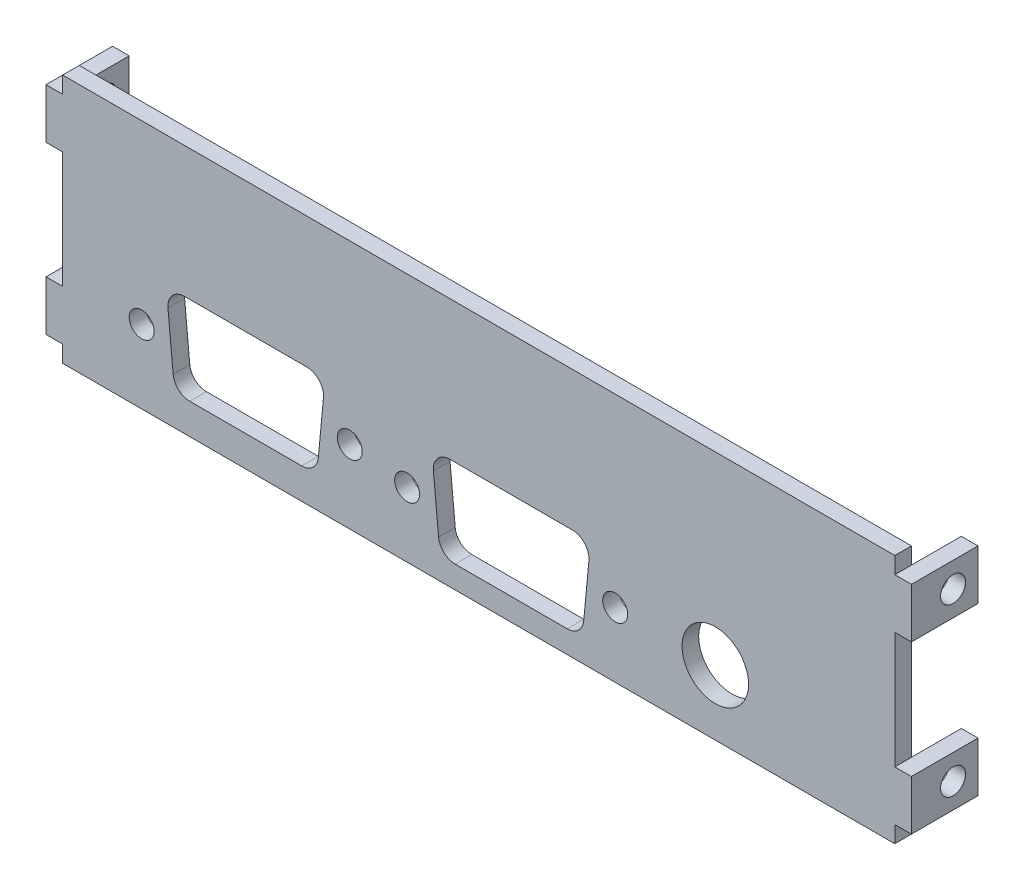
SolidWorks part; units mm, degrees
ref_plane "Front Plane" through (0, 0, 0) normal (0, 0, 1) x (1, 0, 0)
ref_plane "Top Plane" through (0, 0, 0) normal (0, 1, 0) x (1, 0, 0)
ref_plane "Right Plane" through (0, 0, 0) normal (1, 0, 0) x (0, 0, -1)
sketch "Sketch1" plane through (0, 0, 0) normal (0, 0, 1) x (1, 0, 0)
  line L1 (-50, -15) -> (50, -15)
  line L2 (-50, -15) -> (-50, 15)
  line L3 (-50, 15) -> (50, 15)
  line L4 (50, -15) -> (50, 15)
  line L5 (-50, -15) -> (50, 15) construction
  line L6 (-50, 15) -> (50, -15) construction
  point P0 (0, 0)
  dimension "D1" = 30
  dimension "D2" = 100
extrude "Boss-Extrude1" add sketch "Sketch1" along normal blind 2
sketch "Sketch2" plane through (0, 0, 2) normal (0, 0, 1) x (1, 0, 0)
  line L0 (-50, 15) -> (-50, -15) construction
  line L1 (-50, 13) -> (-52, 13)
  line L2 (-50, 13) -> (-50, 7)
  line L3 (-50, 7) -> (-52, 7)
  line L4 (-52, 13) -> (-52, 7)
  line L5 (-51, 7) -> (-51, 13) construction
  line L6 (-50, 10) -> (-52, 10) construction
  line L7 (50, -15) -> (50, 15) construction
  line L8 (-50, -7) -> (-52, -7)
  line L9 (-50, -7) -> (-50, -13)
  line L10 (-50, -13) -> (-52, -13)
  line L11 (-52, -7) -> (-52, -13)
  line L12 (-51, -13) -> (-51, -7) construction
  line L13 (-50, -10) -> (-52, -10) construction
  line L14 (50, 13) -> (52, 13)
  line L15 (50, 13) -> (50, 7)
  line L16 (50, 7) -> (52, 7)
  line L17 (52, 13) -> (52, 7)
  line L18 (51, 7) -> (51, 13) construction
  line L19 (50, 10) -> (52, 10) construction
  line L20 (50, 15) -> (-50, 15) construction
  line L21 (50, -7) -> (52, -7)
  line L22 (50, -7) -> (50, -13)
  line L23 (50, -13) -> (52, -13)
  line L24 (52, -7) -> (52, -13)
  line L25 (51, -13) -> (51, -7) construction
  line L26 (50, -10) -> (52, -10) construction
  line L27 (-50, -15) -> (50, -15) construction
  point P118 (51, 10)
  point P121 (51, -10)
  point P132 (-51, 10)
  point P147 (-51, -10)
  dimension "D1" = 6
  dimension "D2" = 2
  dimension "D3" = 2
  dimension "D4" = 2
  dimension "D5" = 2
  dimension "D6" = 6
  dimension "D7" = 6
  dimension "D8" = 6
  dimension "D9" = 2
  dimension "D10" = 2
  dimension "D11" = 2
  dimension "D12" = 2
extrude "Boss-Extrude2" add sketch "Sketch2" against normal blind 8
sketch "Sketch3" plane through (-52, 0, 0) normal (-1, 0, 0) x (0, 0, 1)
  line L0 (-6, -13) -> (2, -13) construction
  line L1 (-6, 13) -> (0, 13)
  line L2 (-6, 13) -> (-6, 7)
  line L3 (-6, 7) -> (0, 7)
  line L4 (0, 13) -> (0, 7)
  line L5 (-3, 7) -> (-3, 13) construction
  line L6 (-6, 10) -> (0, 10) construction
  line L7 (-6, -7) -> (0, -7)
  line L8 (-6, -7) -> (-6, -13)
  line L9 (-6, -13) -> (0, -13)
  line L10 (0, -7) -> (0, -13)
  line L11 (-3, -13) -> (-3, -7) construction
  line L12 (-6, -10) -> (0, -10) construction
  circle A0 centre (-3, 10) radius 1.5
  circle A1 centre (-3, -10) radius 1.5
  point P14 (0, 0)
  point P136 (-3, -10)
  point P240 (-3, 10)
  dimension "D1" = 3
  dimension "D2" = 3
extrude "Cut-Extrude1" cut sketch "Sketch3" against normal through all contours A0 | A1
sketch "Sketch4" plane through (0, 0, 2) normal (0, 0, 1) x (1, 0, 0)
  line L0 (-35.3524, -0.7122) -> (-20.6476, -0.7122)
  line L1 (-28, -19.7506) -> (-28, -7.2006) construction
  line L2 (-34.7299, -11.3116) -> (-21.2701, -11.3116)
  line L3 (-18.45, -0.7122) -> (-18.45, -17.4256) construction
  line L4 (-37.55, -0.7122) -> (-37.55, -14.1947) construction
  line L5 (-18.6564, -2.9) -> (-19.279, -9.4995)
  line L6 (-37.3436, -2.9) -> (-36.721, -9.4995)
  line L7 (-37.55, -0.7122) -> (-37.55, -0.1761) construction
  line L8 (-3.455, -1.7188) -> (11.2499, -1.7188)
  line L9 (3.8975, -19.8852) -> (3.8975, -8.2006) construction
  line L10 (-2.8323, -12.3122) -> (10.6272, -12.3122)
  line L11 (13.4477, -1.7188) -> (13.4477, -17.5602) construction
  line L12 (-5.6528, -1.7188) -> (-5.6528, -14.8608) construction
  line L13 (13.241, -3.9068) -> (12.6184, -10.5002)
  line L14 (-5.4461, -3.9068) -> (-4.8235, -10.5002)
  line L15 (-5.6528, -1.7188) -> (-5.6528, -1.1761) construction
  line L17 (-8.6048, -7.2) -> (16.3997, -7.2) construction
  line L18 (3.8975, -7.2) -> (3.8975, -8.2006) construction
  line L19 (-40.5023, -6.1998) -> (-15.4977, -6.1998) construction
  line L20 (28.4305, -7.2) -> (16.3997, -7.2) construction
  arc A0 (-19.279, -9.4995) -> (-21.2701, -11.3116) centre (-21.2701, -9.3116) cw
  arc A1 (-34.7299, -11.3116) -> (-36.721, -9.4995) centre (-34.7299, -9.3116) cw
  arc A2 (-18.6564, -2.9) -> (-20.6476, -0.7122) centre (-20.6476, -2.7122) ccw
  arc A3 (-37.3436, -2.9) -> (-35.3524, -0.7122) centre (-35.3524, -2.7122) cw
  circle A4 centre (-40.5023, -6.1998) radius 1.5
  circle A5 centre (-15.4977, -6.1998) radius 1.5
  arc A6 (12.6184, -10.5002) -> (10.6272, -12.3122) centre (10.6272, -10.3122) cw
  arc A7 (-2.8323, -12.3122) -> (-4.8235, -10.5002) centre (-2.8323, -10.3122) cw
  arc A8 (13.241, -3.9068) -> (11.2499, -1.7188) centre (11.2499, -3.7188) ccw
  arc A9 (-5.4461, -3.9068) -> (-3.455, -1.7188) centre (-3.455, -3.7188) cw
  circle A10 centre (-8.6048, -7.2) radius 1.5
  circle A11 centre (16.3997, -7.2) radius 1.5
  circle A12 centre (28.4305, -7.2) radius 4
  point P4 (-28, -0.7122)
  point P8 (-37.0323, -6.1998)
  point P10 (-18.9677, -6.1998)
  point P32 (3.8975, -1.7188)
  point P36 (-5.1348, -7.2035)
  point P38 (12.9297, -7.2035)
  dimension "D2" = 2
  dimension "D4" = 3
  dimension "D8" = 2
  dimension "D10" = 3
  dimension "D21" = 3
  dimension "D22" = 1.0006
  dimension "D23" = 3
  dimension "D28" = 8
  dimension "D1" = 5.389
  dimension "D3" = 7.3524
  dimension "D5" = 3.47
  dimension "D6" = 3.47
  dimension "D7" = 5.395
  dimension "D9" = 7.3524
  dimension "D11" = 3.47
  dimension "D12" = 3.47
  dimension "D13" = 28
  dimension "D14" = 7.2006
  dimension "D15" = 3.8975
  dimension "D16" = 7.0245
  dimension "D17" = 10.5934
  dimension "D18" = 10.5994
  dimension "D19" = 25.0045
  dimension "D20" = 1.0006
  dimension "D24" = 25.0046
  dimension "D25" = 1.0009
  dimension "D26" = 4.111
  dimension "D27" = 7.2
  dimension "D29" = 28.4305
extrude "Cut-Extrude2" cut sketch "Sketch4" against normal up to next
